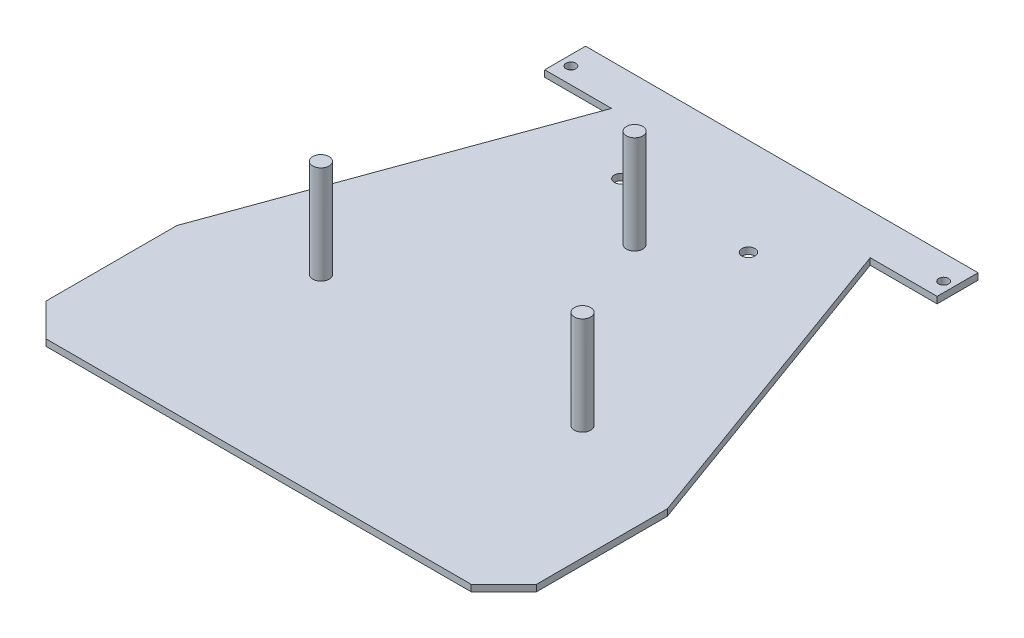
SolidWorks part; units mm, degrees
ref_plane "Front Plane" through (0, 0, 0) normal (0, 0, 1) x (1, 0, 0)
ref_plane "Top Plane" through (0, 0, 0) normal (0, 1, 0) x (1, 0, 0)
ref_plane "Right Plane" through (0, 0, 0) normal (1, 0, 0) x (0, 0, -1)
sketch "Sketch1" plane through (0, 0, 0) normal (0, 1, 0) x (1, 0, 0)
  line L0 (-75, -70) -> (-65, -80)
  line L1 (-65, -80) -> (65, -80)
  line L2 (-75, -70) -> (-75, -30)
  line L3 (-35, 80) -> (35, 80)
  line L4 (75, -70) -> (75, -30)
  line L5 (-75, -80) -> (75, 80) construction
  line L6 (-75, 80) -> (75, -80) construction
  line L7 (75, -70) -> (65, -80)
  line L8 (-75, -30) -> (-35, 80)
  line L9 (35, 80) -> (75, -30)
  point P0 (0, 0)
  dimension "D1" = 160
  dimension "D2" = 150
  dimension "D3" = 10
  dimension "D4" = 10
  dimension "D5" = 10
  dimension "D6" = 10
  dimension "D7" = 50
  dimension "D8" = 50
  dimension "D9" = 40
  dimension "40" = 40
extrude "Boss-Extrude1" add sketch "Sketch1" along normal blind 2
sketch "Sketch2" plane through (0, 0, 0) normal (0, -1, 0) x (1, 0, 0)
  line L0 (0, -80) -> (0, 80) construction
  line L1 (35, -80) -> (-35, -80) construction
  line L2 (-65, 80) -> (65, 80) construction
  circle A0 centre (-19.5, -50.3127) radius 2
  circle A1 centre (19.5, -50.3127) radius 2
  dimension "D1" = 4
  dimension "D2" = 4
  dimension "D3" = 39
  dimension "D4" = 19.5
extrude "Cut-Extrude1" cut sketch "Sketch2" against normal up to next
sketch "Sketch3" plane through (0, 0, 0) normal (0, -1, 0) x (1, 0, 0)
  line L0 (-35, -80) -> (-60, -80)
  line L1 (35, -80) -> (-35, -80) construction
  line L2 (-35, -80) -> (-75, 30) construction
  line L3 (-60, -80) -> (-60, -67.5)
  line L4 (-60, -67.5) -> (60, -67.5)
  line L5 (60, -67.5) -> (60, -80)
  line L6 (60, -80) -> (-35, -80)
  line L7 (0, -80) -> (0, 80) construction
  line L8 (-65, 80) -> (65, 80) construction
  point P6 (60, -73.75)
  dimension "D1" = 12.5
  dimension "D2" = 12.5
  dimension "D3" = 120
  dimension "D4" = 60
extrude "Boss-Extrude2" add sketch "Sketch3" against normal blind 2
sketch "Sketch5" plane through (0, 2, 0) normal (0, 1, 0) x (1, 0, 0)
  line L0 (-39.5455, 67.5) -> (-60, 67.5) construction
  line L1 (60, 67.5) -> (39.5455, 67.5) construction
  circle A2 centre (57, 72.5) radius 1.5
  circle A3 centre (-57, 72.5) radius 1.5
  dimension "D1" = 5
  dimension "D2" = 5
extrude "Cut-Extrude2" cut sketch "Sketch5" against normal up to next
sketch "Sketch6" plane through (0, 2, 0) normal (0, 1, 0) x (1, 0, 0)
  circle A0 centre (-40, -20.9353) radius 2.5
  circle A1 centre (40, -20.9353) radius 2.5
  circle A2 centre (0, 35) radius 2.5
  point P6 (0, 0)
  point P8 (0, 0)
  dimension "D1" = 5
  dimension "D2" = 5
  dimension "D3" = 5
  dimension "D4" = 40
  dimension "D5" = 40
  dimension "D6" = 35
extrude "Boss-Extrude3" add sketch "Sketch6" along normal blind 30
